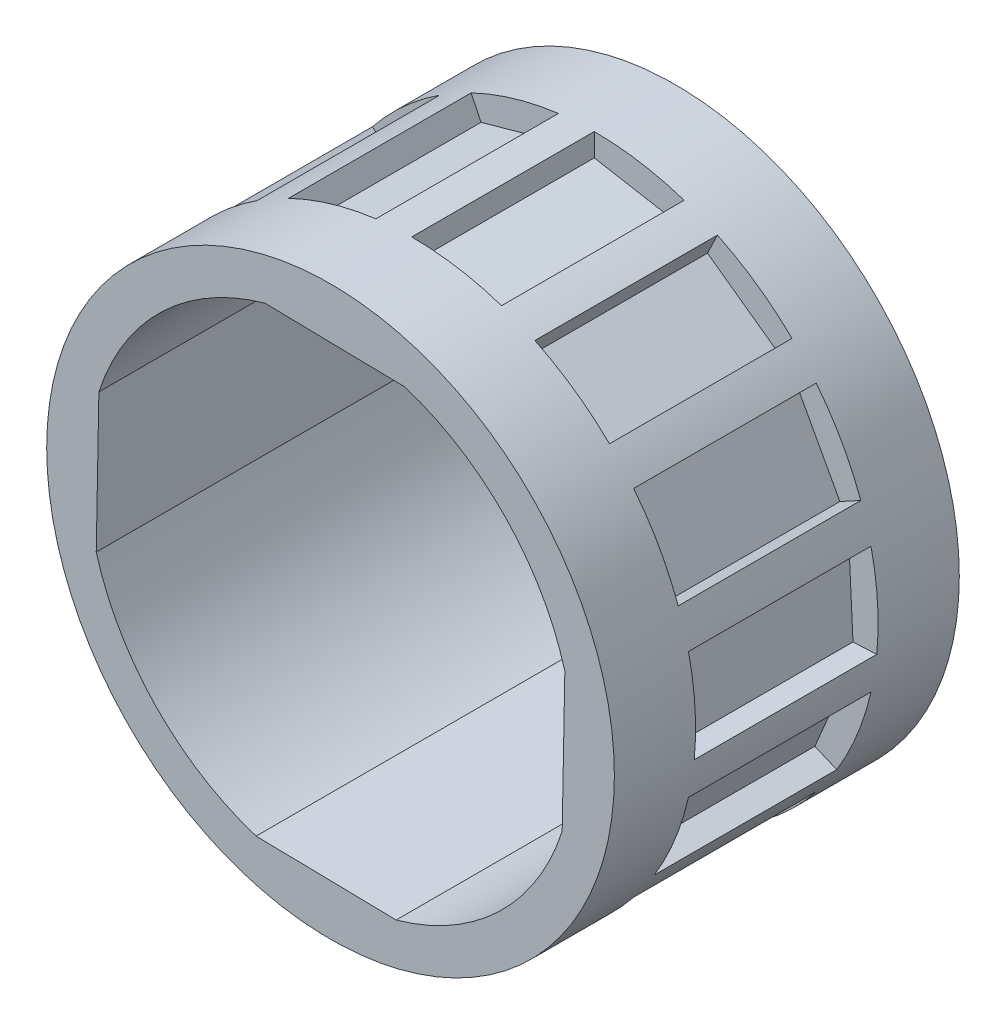
SolidWorks part; units mm, degrees
material "Ductile Iron"
ref_plane "Front Plane" through (0, 0, 0) normal (0, 0, 1) x (1, 0, 0)
ref_plane "Top Plane" through (0, 0, 0) normal (0, 1, 0) x (1, 0, 0)
ref_plane "Right Plane" through (0, 0, 0) normal (1, 0, 0) x (0, 0, -1)
sketch "Sketch1" plane through (0, 0, 0) normal (0, 0, 1) x (1, 0, 0)
  line L4 (0, 9.081) -> (2.9813, 8.5517)
  line L79 (3.1261, 9.3671) -> (2.9813, 8.5517)
  line L83 (6.8808, 7.0831) -> (6.3965, 6.4112)
  line L116 (6.3965, 6.4112) -> (6.8808, 7.0831)
  line L117 (9.2726, 3.3962) -> (8.5448, 3.001)
  line L118 (8.5448, 3.001) -> (9.2726, 3.3962)
  line L119 (9.8279, -0.9633) -> (9.0007, -1.0037)
  line L120 (0, 9.081) -> (0, 9.875)
  line L121 (0, 9.081) -> (2.9813, 8.5517)
  line L124 (3.9401, 8.1817) -> (6.3965, 6.4112)
  line L125 (3.9401, 8.1817) -> (4.2846, 8.8971)
  line L127 (7.0998, 5.6619) -> (8.5448, 3.001)
  line L128 (7.0998, 5.6619) -> (7.7206, 6.157)
  line L130 (8.8533, 2.0207) -> (9.0007, -1.0037)
  line L131 (8.8533, 2.0207) -> (9.6274, 2.1974)
  line L133 (8.8533, -2.0207) -> (7.6739, -4.8095)
  line L134 (8.8533, -2.0207) -> (9.6274, -2.1974)
  line L136 (7.0998, -5.6619) -> (4.8271, -7.6628)
  line L137 (7.0998, -5.6619) -> (7.7206, -6.157)
  line L139 (3.9401, -8.1817) -> (1.0243, -8.9983)
  line L140 (3.9401, -8.1817) -> (4.2846, -8.8971)
  line L142 (0, -9.081) -> (-2.9813, -8.5517)
  line L143 (0, -9.081) -> (0, -9.875)
  line L145 (-3.9401, -8.1817) -> (-6.3965, -6.4112)
  line L146 (-3.9401, -8.1817) -> (-4.2846, -8.8971)
  line L148 (-7.0998, -5.6619) -> (-8.5448, -3.001)
  line L149 (-7.0998, -5.6619) -> (-7.7206, -6.157)
  line L151 (-8.8533, -2.0207) -> (-9.0007, 1.0037)
  line L152 (-8.8533, -2.0207) -> (-9.6274, -2.1974)
  line L154 (-8.8533, 2.0207) -> (-7.6739, 4.8095)
  line L155 (-8.8533, 2.0207) -> (-9.6274, 2.1974)
  line L157 (-7.0998, 5.6619) -> (-4.8271, 7.6628)
  line L158 (-7.0998, 5.6619) -> (-7.7206, 6.157)
  line L160 (-3.9401, 8.1817) -> (-1.0243, 8.9983)
  line L161 (-3.9401, 8.1817) -> (-4.2846, 8.8971)
  line L164 (2.5893, 8.0593) -> (-2.283, 8.1513)
  line L165 (8.0593, -2.5893) -> (8.1513, 2.283)
  line L166 (-2.5893, -8.0593) -> (2.283, -8.1513)
  line L167 (-8.0593, 2.5893) -> (-8.1513, -2.283)
  line L168 (8.4366, -5.1321) -> (7.6739, -4.8095)
  line L169 (7.6739, -4.8095) -> (8.4366, -5.1321)
  line L170 (5.3744, -8.2844) -> (4.8271, -7.6628)
  line L171 (1.2477, -9.7959) -> (1.0243, -8.9983)
  line L173 (1.0243, -8.9983) -> (1.2477, -9.7959)
  line L174 (-3.1261, -9.3671) -> (-2.9813, -8.5517)
  line L175 (-2.9813, -8.5517) -> (-3.1261, -9.3671)
  line L176 (-6.8808, -7.0831) -> (-6.3965, -6.4112)
  line L177 (-6.3965, -6.4112) -> (-6.8808, -7.0831)
  line L178 (-9.2726, -3.3962) -> (-8.5448, -3.001)
  line L179 (-8.5448, -3.001) -> (-9.2726, -3.3962)
  line L180 (-9.8279, 0.9633) -> (-9.0007, 1.0037)
  line L181 (-9.0007, 1.0037) -> (-9.8279, 0.9633)
  line L182 (-8.4366, 5.1321) -> (-7.6739, 4.8095)
  line L183 (-7.6739, 4.8095) -> (-8.4366, 5.1321)
  line L184 (-5.3744, 8.2844) -> (-4.8271, 7.6628)
  line L185 (-4.8271, 7.6628) -> (-5.3744, 8.2844)
  line L186 (-1.2477, 9.7959) -> (-1.0243, 8.9983)
  line L187 (-1.0243, 8.9983) -> (-1.2477, 9.7959)
  arc A62 (0, 9.875) -> (-1.2477, 9.7959) centre (0, 0) ccw
  arc A65 (4.2846, 8.8971) -> (3.1261, 9.3671) centre (0, 0) ccw
  arc A66 (-4.2846, 8.8971) -> (-5.3744, 8.2844) centre (0, 0) ccw
  arc A67 (-7.7206, 6.157) -> (-8.4366, 5.1321) centre (0, 0) ccw
  arc A68 (-9.6274, 2.1974) -> (-9.8279, 0.9633) centre (0, 0) ccw
  arc A69 (-9.6274, -2.1974) -> (-9.2726, -3.3962) centre (0, 0) ccw
  arc A70 (-7.7206, -6.157) -> (-6.8808, -7.0831) centre (0, 0) ccw
  arc A71 (-4.2846, -8.8971) -> (-3.1261, -9.3671) centre (0, 0) ccw
  arc A72 (0, -9.875) -> (1.2477, -9.7959) centre (0, 0) ccw
  arc A73 (4.2846, -8.8971) -> (5.3744, -8.2844) centre (0, 0) ccw
  arc A74 (7.7206, -6.157) -> (8.4366, -5.1321) centre (0, 0) ccw
  arc A75 (9.6274, -2.1974) -> (9.8279, -0.9633) centre (0, 0) ccw
  arc A76 (9.6274, 2.1974) -> (9.2726, 3.3962) centre (0, 0) ccw
  arc A77 (7.7206, 6.157) -> (6.8808, 7.0831) centre (0, 0) ccw
  arc A78 (-2.283, 8.1513) -> (-8.0593, 2.5893) centre (0, 0) ccw
  arc A79 (8.1513, 2.283) -> (2.5893, 8.0593) centre (0, 0) ccw
  arc A80 (2.283, -8.1513) -> (8.0593, -2.5893) centre (0, 0) ccw
  arc A81 (-8.1513, -2.283) -> (-2.5893, -8.0593) centre (0, 0) ccw
  point P81 (0, 0)
  point P96 (0, 0)
  point P135 (0, 0)
  point P146 (0, 0)
  point P152 (0, 0)
  dimension "D7" = 14
  dimension "D8" = 4
extrude "Boss-Extrude1" add sketch "Sketch1" along normal blind 6.35
sketch "Sketch3" plane through (0, 0, 6.35) normal (0, 0, 1) x (1, 0, 0)
  line L0 (-2.283, 8.1513) -> (2.5893, 8.0593)
  line L1 (8.1513, 2.283) -> (8.0593, -2.5893)
  line L2 (2.283, -8.1513) -> (-2.5893, -8.0593)
  line L3 (-8.1513, -2.283) -> (-8.0593, 2.5893)
  arc A0 (-2.283, 8.1513) -> (-8.0593, 2.5893) centre (0, 0) ccw
  circle A1 centre (0, 0) radius 9.875
  arc A2 (-8.1513, -2.283) -> (-2.5893, -8.0593) centre (0, 0) ccw
  arc A3 (2.283, -8.1513) -> (8.0593, -2.5893) centre (0, 0) ccw
  arc A4 (8.1513, 2.283) -> (2.5893, 8.0593) centre (0, 0) ccw
  point P17 (0, 0)
  dimension "D1" = 4
extrude "Boss-Extrude3" add sketch "Sketch3" along normal blind 2.825
sketch "Sketch7" plane through (0, 0, 0) normal (0, 0, -1) x (-1, 0, 0)
  line L0 (-2.5893, 8.0593) -> (2.283, 8.1513)
  line L1 (8.0593, 2.5893) -> (8.1513, -2.283)
  line L2 (2.5893, -8.0593) -> (-2.283, -8.1513)
  line L3 (-8.0593, -2.5893) -> (-8.1513, 2.283)
  circle A0 centre (0, 0) radius 9.875
  arc A1 (-2.5893, 8.0593) -> (-8.1513, 2.283) centre (0, 0) ccw
  arc A2 (-8.0593, -2.5893) -> (-2.283, -8.1513) centre (0, 0) ccw
  arc A3 (2.5893, -8.0593) -> (8.1513, -2.283) centre (0, 0) ccw
  arc A4 (8.0593, 2.5893) -> (2.283, 8.1513) centre (0, 0) ccw
  point P17 (0, 0)
  dimension "D1" = 4
extrude "Boss-Extrude5" add sketch "Sketch7" along normal blind 2.825
